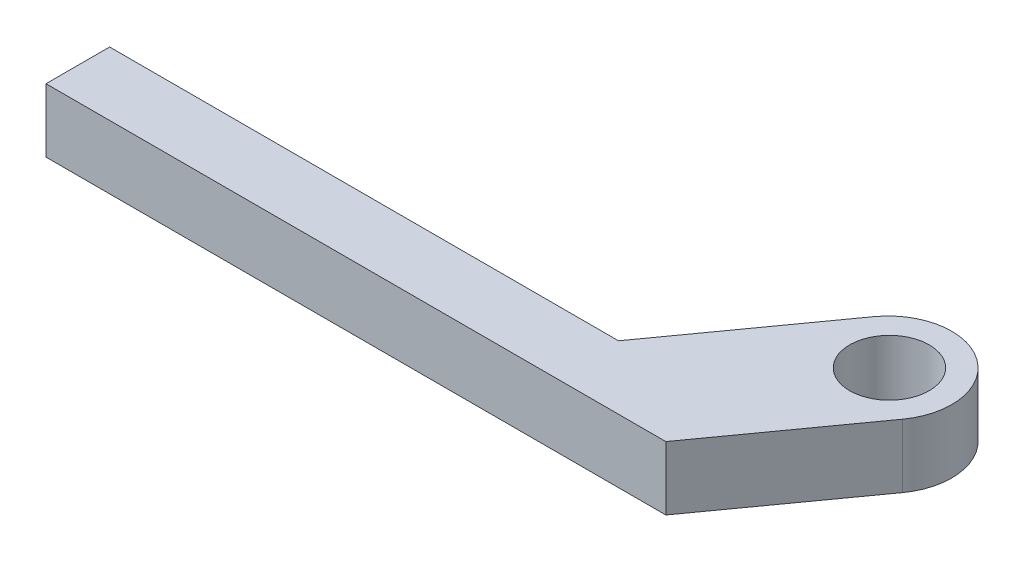
SolidWorks part; units mm, degrees
ref_plane "Front Plane" through (0, 0, 0) normal (0, 0, 1) x (1, 0, 0)
ref_plane "Top Plane" through (0, 0, 0) normal (0, 1, 0) x (1, 0, 0)
ref_plane "Right Plane" through (0, 0, 0) normal (1, 0, 0) x (0, 0, -1)
sketch "Sketch2" plane through (0, 0, 0) normal (0, 1, 0) x (1, 0, 0)
  line L5 (-10.6389, -35.243) -> (0.0062, -20.4255)
  line L7 (-61.4389, -41.593) -> (-10.6389, -41.593)
  line L8 (-61.4389, -41.593) -> (-61.4389, -35.243)
  line L9 (-61.4389, -35.243) -> (-10.6389, -35.243)
  line L10 (-10.6389, -41.593) -> (-10.6389, -35.243) construction
  line L11 (-61.4389, -41.593) -> (-10.6389, -35.243) construction
  line L12 (-61.4389, -35.243) -> (-10.6389, -41.593) construction
  line L14 (-10.6389, -41.593) -> (0.4368, -41.593)
  line L18 (10.3205, -27.8354) -> (0.4368, -41.593)
  line L19 (0.0062, -20.4255) -> (10.3205, -27.8354) construction
  line L20 (5.1633, -17.7805) -> (-45.4817, -17.7805) construction
  arc A2 (0.0062, -20.4255) -> (10.3205, -27.8354) centre (5.1633, -24.1305) cw
  point P5 (-36.0389, -38.418)
  dimension "D2" = 12.7
  dimension "D3" = 17.4625
  dimension "D4" = 6.35
  dimension "D10" = 50.8
extrude "Boss-Extrude1" add sketch "Sketch2" along normal blind 6.35
hole_wizard "3/8-16 Tapped Hole1" positions "Sketch3" profile "Sketch4" tap size "3/8-16" standard "ANSI Inch"
sketch "Sketch3" plane through (0, 6.35, 0) normal (0, 1, 0) x (1, 0, 0)
  line L0 (0.4368, -41.593) -> (10.3205, -27.8354) construction
  arc A0 (10.3205, -27.8354) -> (0.0062, -20.4255) centre (5.1633, -24.1305) ccw construction
  point P0 (5.2187, -24.0534)
  point P6 (8.8683, -18.9734)
  dimension "D1" = 5.08
  dimension "D2" = 6.35
sketch "Sketch4" plane through (5.2187, 6.35, 24.0534) normal (1, 0, 0) x (0, 0, 1)
  line L0 (0, 0) -> (0, 8.7347)
  line L1 (0, 8.7347) -> (3.9687, 6.35)
  line L2 (3.9687, 6.35) -> (3.9688, 0)
  line L5 (3.9688, 0) -> (0, 0)
  line L10 (0, 8.7347) -> (-3.9688, 6.35) construction
  line L11 (0, -6.35) -> (0, 107.95) construction
  dimension "Tap Drill Dia." = 7.9375
  dimension "Tap Drill Depth" = 6.35
  dimension "Drill Angle" = 118
cosmetic thread "Hole Thread1"
sketch "Sketch5" plane through (0, 6.35, 0) normal (0, 1, 0) x (1, 0, 0)
  line L0 (5.1633, -17.7805) -> (-38.0048, -17.7805) construction
  arc A0 (10.3205, -27.8354) -> (0.0062, -20.4255) centre (5.1633, -24.1305) ccw construction
sketch "Sketch7" plane through (0, 0, 0) normal (0, -1, 0) x (1, 0, 0)
  line L5 (10.3205, 27.8354) -> (0.4368, 41.593)
  line L6 (0.4368, 41.593) -> (-61.4389, 41.593)
  line L7 (-61.4389, 41.593) -> (-61.4389, 35.243)
  line L8 (-61.4389, 35.243) -> (-10.6389, 35.243)
  line L9 (-10.6389, 35.243) -> (0.0062, 20.4255)
  line L10 (10.3205, 27.8354) -> (0.4368, 41.593)
  line L11 (0.4368, 41.593) -> (-61.4389, 41.593)
  line L12 (-61.4389, 41.593) -> (-61.4389, 35.243)
  line L13 (-61.4389, 35.243) -> (-10.6389, 35.243)
  line L14 (-10.6389, 35.243) -> (0.0062, 20.4255)
  arc A1 (0.0062, 20.4255) -> (10.3205, 27.8354) centre (5.1633, 24.1305) ccw
  arc A2 (0.0062, 20.4255) -> (10.3205, 27.8354) centre (5.1633, 24.1305) ccw
  dimension "D1" = 0
